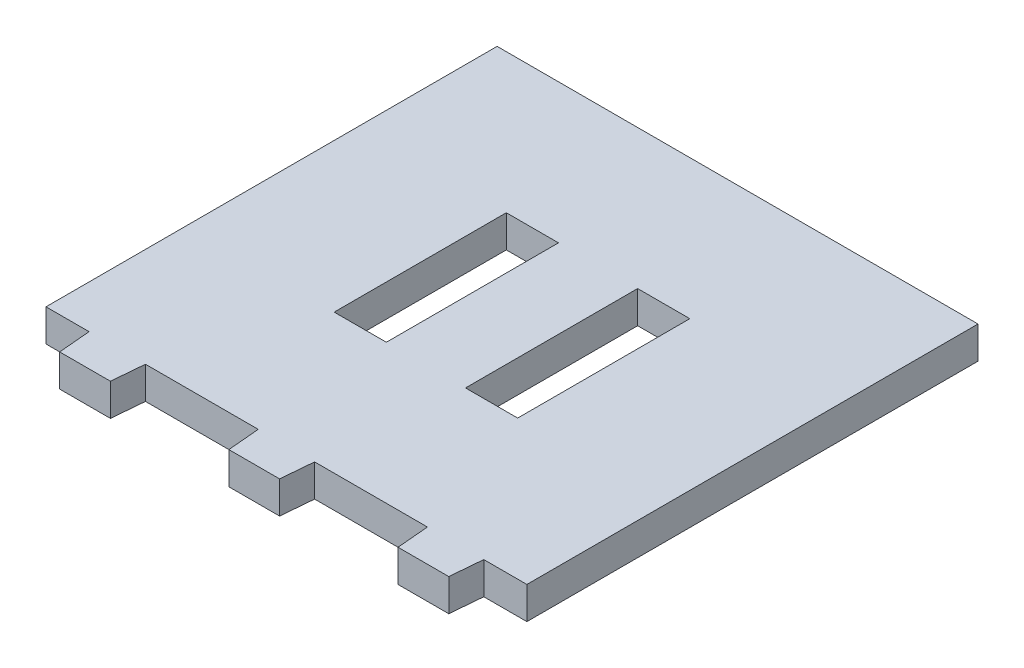
SolidWorks part; units mm, degrees
ref_plane "Front Plane" through (0, 0, 0) normal (0, 0, 1) x (1, 0, 0)
ref_plane "Top Plane" through (0, 0, 0) normal (0, 1, 0) x (1, 0, 0)
ref_plane "Right Plane" through (0, 0, 0) normal (1, 0, 0) x (0, 0, -1)
sketch "Sketch2" plane through (0, 0, 0) normal (0, 1, 0) x (1, 0, 0)
  line L0 (0, 0) -> (0, -127889.9036) construction
  line L1 (-42.6398, 40) -> (42.6398, 40)
  line L2 (-42.6398, 40) -> (-42.6398, -40)
  line L3 (-42.6398, -40) -> (42.6398, -40)
  line L4 (42.6398, 40) -> (42.6398, -40)
  line L5 (-42.6398, 40) -> (42.6398, -40) construction
  line L6 (-42.6398, -40) -> (42.6398, 40) construction
  line L7 (-5, -40) -> (5, -40)
  line L8 (5, -40) -> (4.5, -45.715)
  line L9 (4.5, -45.715) -> (-4.5, -45.715)
  line L10 (-4.5, -45.715) -> (-5, -40)
  line L11 (0, -40) -> (0, -96.5171) construction
  line L12 (-35, -40) -> (-25, -40)
  line L13 (-25, -40) -> (-25.5, -45.715)
  line L14 (-25.5, -45.715) -> (-34.5, -45.715)
  line L15 (-34.5, -45.715) -> (-35, -40)
  line L16 (-30, -40) -> (-30, -95.4613) construction
  line L21 (-60, -40) -> (-60, -98.6867) construction
  line L22 (60, -40) -> (60, -98.6867) construction
  line L23 (30, -40) -> (30, -95.4613) construction
  line L28 (34.5, -45.715) -> (35, -40)
  line L29 (25.5, -45.715) -> (34.5, -45.715)
  line L30 (25, -40) -> (25.5, -45.715)
  line L31 (35, -40) -> (25, -40)
  line L32 (16.2716, -15.2642) -> (7.0186, -15.2642)
  line L33 (-16.2716, 15.2642) -> (-7.0186, 15.2642)
  line L34 (-16.2716, 15.2642) -> (-16.2716, -15.2642)
  line L35 (-16.2716, -15.2642) -> (-7.0186, -15.2642)
  line L36 (-7.0186, 15.2642) -> (-7.0186, -15.2642)
  line L37 (7.0186, 15.2642) -> (7.0186, -15.2642)
  line L38 (16.2716, 15.2642) -> (7.0186, 15.2642)
  line L39 (16.2716, 15.2642) -> (16.2716, -15.2642)
  point P0 (0, 0)
  point P24 (0, -45.715)
  point P25 (-30, -45.715)
  dimension "D2" = 9
  dimension "D3" = 5.715
  dimension "D4" = 85.2796
  dimension "D9" = 80
  dimension "D10" = 10
  dimension "D5" = 10
  dimension "D6" = 9
  dimension "D7" = 5.715
  dimension "D8" = 30
extrude "Boss-Extrude1" add sketch "Sketch2" along normal blind 5.715
equation "\"toothBaseWidth\"=0.01"
equation "\"toothEndWidth\"=0.009"
equation "\"toothLength\"= 0.005715"
equation "\"D2@Sketch2\"= \"toothEndWidth\""
equation "\"D3@Sketch2\"= \"toothLength\""
equation "\"holeWidth\" = 0.009"
equation "\"motorHolderToothSeparation\" = 0.01"
equation "\"magnetHolderToothSeparation\" = 0.02"
equation "\"D10@Sketch2\"=\"toothBaseWidth\""
equation "\"D5@Sketch2\"=\"toothBaseWidth\""
equation "\"D6@Sketch2\"=\"toothEndWidth\""
equation "\"D7@Sketch2\"=\"toothLength\""
equation "\"magnetWidth\" = 0.0127"
equation "\"quarterInch\" = 0.005715"
equation "\"coilThickness\" = 0.0254"
equation "\"coilOuterDiameter\" = 0.0508"
equation "\"legoThickness\" = 0.008"
equation "\"legoWidth\" = 0.016"
equation "\"D1@Boss-Extrude1\"=\"quarterInch\""
